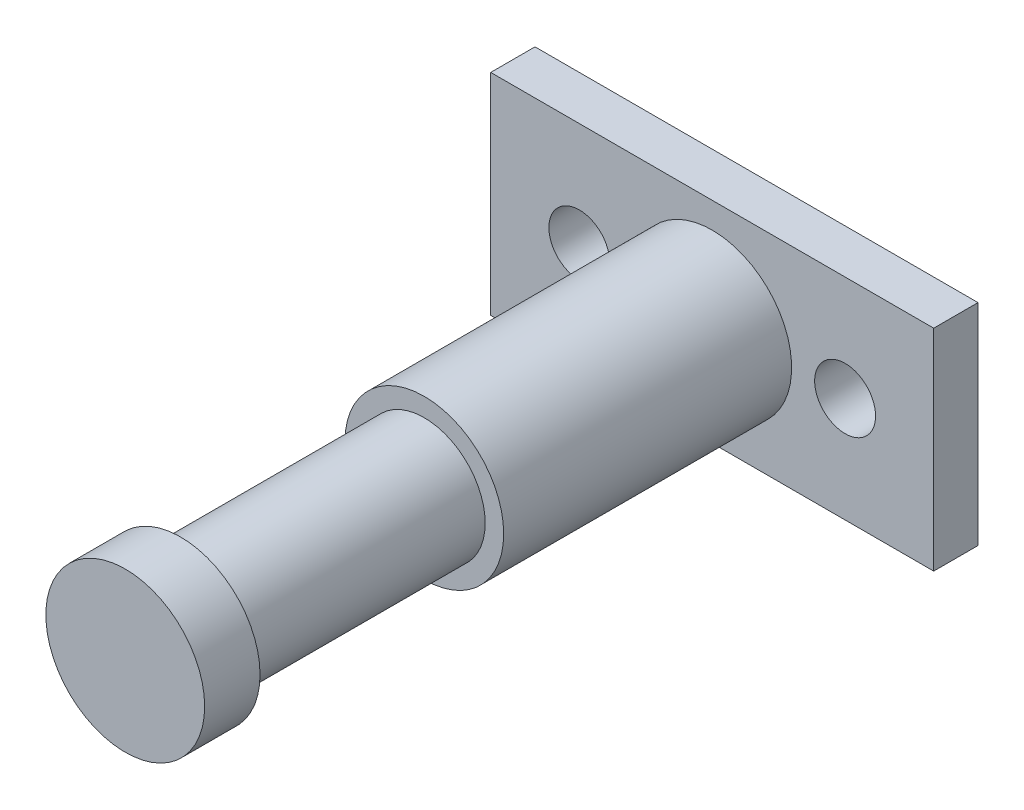
SolidWorks part; units mm, degrees
material "6063-T5"
ref_plane "Front Plane" through (0, 0, 0) normal (0, 0, 1) x (1, 0, 0)
ref_plane "Top Plane" through (0, 0, 0) normal (0, 1, 0) x (1, 0, 0)
ref_plane "Right Plane" through (0, 0, 0) normal (1, 0, 0) x (0, 0, -1)
sketch "Sketch1" plane through (0, 0, 0) normal (0, 0, 1) x (1, 0, 0)
  line L1 (-20, -9.5) -> (20, -9.5)
  line L2 (-20, -9.5) -> (-20, 9.5)
  line L3 (-20, 9.5) -> (20, 9.5)
  line L4 (20, -9.5) -> (20, 9.5)
  line L5 (-20, -9.5) -> (20, 9.5) construction
  line L6 (-20, 9.5) -> (20, -9.5) construction
  circle A1 centre (12, 0) radius 2.75
  circle A2 centre (-12, 0) radius 2.75
  point P0 (0, 0)
  dimension "D4" = 5.5
  dimension "D1" = 19
  dimension "D2" = 40
  dimension "D5" = 8
  dimension "D6" = 8
extrude "Boss-Extrude1" add sketch "Sketch1" against normal blind 4
sketch "Sketch2" plane through (0, 0, 0) normal (0, 0, 1) x (1, 0, 0)
  circle A0 centre (0, 0) radius 7.1705
  dimension "D1" = 14.341
extrude "Boss-Extrude2" add sketch "Sketch2" along normal blind 26
sketch "Sketch3" plane through (0, 0, 26) normal (0, 0, 1) x (1, 0, 0)
  circle A0 centre (0, 0) radius 5.5
  dimension "D1" = 11
extrude "Boss-Extrude3" add sketch "Sketch3" along normal blind 22
sketch "Sketch4" plane through (0, 0, 48) normal (0, 0, 1) x (1, 0, 0)
  circle A0 centre (0, 0) radius 7.1705
  circle A1 centre (0, 0) radius 7.1705 construction
extrude "Boss-Extrude4" add sketch "Sketch4" along normal blind 5
